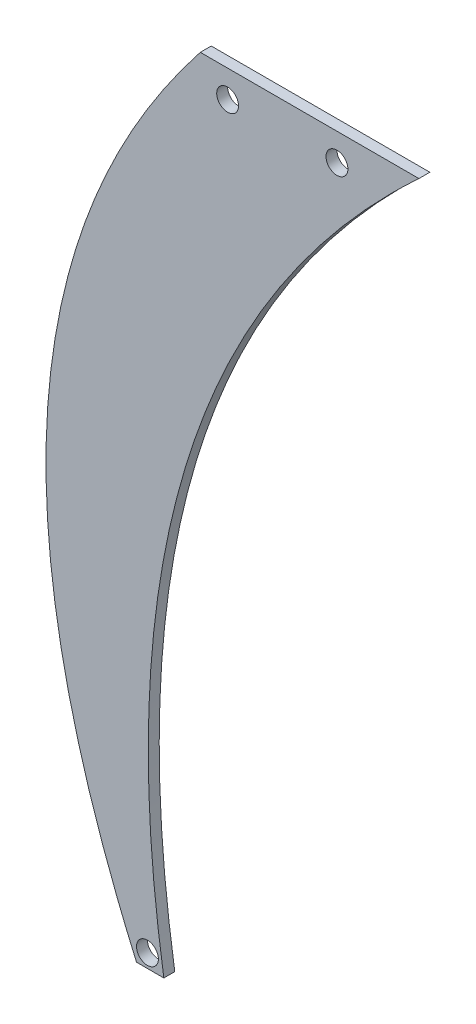
SolidWorks part; units mm, degrees
material "Стеклотекстолит"
ref_plane "Спереди" through (0, 0, 0) normal (0, 0, 1) x (1, 0, 0)
ref_plane "Сверху" through (0, 0, 0) normal (0, 1, 0) x (1, 0, 0)
ref_plane "Справа" through (0, 0, 0) normal (1, 0, 0) x (0, 0, -1)
sketch "Эскиз1" plane through (0, 0, 0) normal (0, 0, 1) x (1, 0, 0)
  line L0 (0, 0) -> (40, 0)
  line L1 (-11.6703, -150) -> (-6.6703, -150)
  spline S0 degree 2 poles (0, 0) (-49.8541, -63.236) (-11.6703, -150) knots 0 0 0 1 1 1
  spline S1 degree 2 poles (40, 0) (-21.3893, -56.8181) (-6.6703, -150) knots 0 0 0 1 1 1
  dimension "D1" = 40
  dimension "D2" = 5
  dimension "D3" = 150
extrude "Бобышка-Вытянуть1" add sketch "Эскиз1" along normal blind 2
sketch "Эскиз2" plane through (0, 0, 2) normal (0, 0, 1) x (1, 0, 0)
  line L0 (5, -5) -> (25, -5) construction
  line L1 (40, 0) -> (0, 0) construction
  line L3 (-11.6703, -150) -> (-6.6703, -150) construction
  circle A0 centre (5, -5) radius 2
  circle A1 centre (25, -5) radius 2
  circle A2 centre (-9.6703, -147.5) radius 2
  dimension "D1" = 4
  dimension "D5" = 4
  dimension "D2" = 5
  dimension "D3" = 20
  dimension "D4" = 15
  dimension "D6" = 2
  dimension "D7" = 2.5
extrude "Вырез-Вытянуть1" cut sketch "Эскиз2" against normal through all
equation "\"thick\"= \"текстолит@сборка.SLDASM\""
equation "\"D1@Бобышка-Вытянуть1\"=\"thick\""
